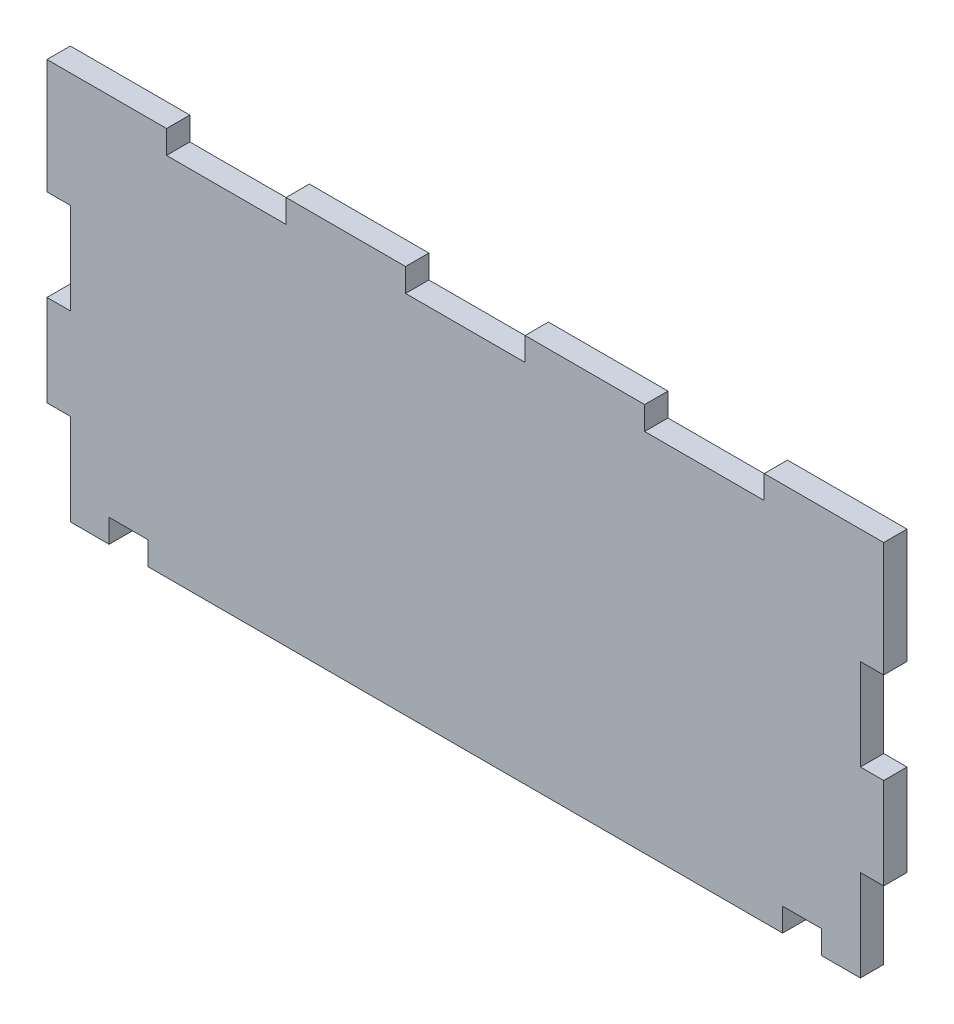
SolidWorks part; units mm, degrees
ref_plane "Alzado" through (0, 0, 0) normal (0, 0, 1) x (1, 0, 0)
ref_plane "Planta" through (0, 0, 0) normal (0, 1, 0) x (1, 0, 0)
ref_plane "Vista lateral" through (0, 0, 0) normal (1, 0, 0) x (0, 0, -1)
sketch "Croquis1" plane through (0, 0, 0) normal (0, 0, 1) x (1, 0, 0)
  line L0 (-76.15, 28.8494) -> (-76.15, -51.02) construction
  line L1 (-79.15, 18.6361) -> (33.46, 18.6361) construction
  line L2 (-79.15, 18.6361) -> (-79.15, -31.3639) construction
  line L3 (-79.15, -31.3639) -> (33.46, -31.3639) construction
  line L4 (33.46, 18.6361) -> (33.46, -31.3639) construction
  line L5 (30.46, 26.8438) -> (30.46, -48.3082) construction
  line L6 (-85.6573, -28.3639) -> (41.9564, -28.3639) construction
  line L7 (-99.0946, 15.6361) -> (68.6346, 15.6361) construction
  line L8 (-71.15, -28.3639) -> (-71.15, -31.3639)
  line L9 (25.46, -28.3639) -> (25.46, -31.3639)
  line L10 (-71.15, -31.3639) -> (25.46, -31.3639)
  line L11 (-71.15, -28.3639) -> (-76.15, -28.3639)
  line L12 (-76.15, -28.3639) -> (-76.15, -31.3639)
  line L13 (-76.15, -31.3639) -> (-79.15, -31.3639)
  line L14 (25.46, -28.3639) -> (30.46, -28.3639)
  line L15 (30.46, -28.3639) -> (30.46, -31.3639)
  line L16 (30.46, -31.3639) -> (33.46, -31.3639)
  line L17 (33.46, -31.3639) -> (33.46, -19.6139)
  line L18 (33.46, -19.6139) -> (30.46, -19.6139)
  line L19 (30.46, -19.6139) -> (30.46, -7.8639)
  line L20 (30.46, -7.8639) -> (33.46, -7.8639)
  line L21 (33.46, -7.8639) -> (33.46, 3.8861)
  line L22 (33.46, 3.8861) -> (30.46, 3.8861)
  line L23 (30.46, 3.8861) -> (30.46, 15.6361)
  line L24 (30.46, 15.6361) -> (15.23, 15.6361)
  line L25 (15.23, 15.6361) -> (15.23, 18.6361)
  line L26 (15.23, 18.6361) -> (0, 18.6361)
  line L27 (0, 18.6361) -> (0, 15.6361)
  line L28 (0, 15.6361) -> (-15.23, 15.6361)
  line L29 (-15.23, 15.6361) -> (-15.23, 18.6361)
  line L30 (-15.23, 18.6361) -> (-30.46, 18.6361)
  line L31 (-30.46, 18.6361) -> (-30.46, 15.6361)
  line L32 (-30.46, 15.6361) -> (-45.69, 15.6361)
  line L33 (-45.69, 15.6361) -> (-45.69, 18.6361)
  line L34 (-45.69, 18.6361) -> (-60.92, 18.6361)
  line L35 (-60.92, 18.6361) -> (-60.92, 15.6361)
  line L36 (-60.92, 15.6361) -> (-76.15, 15.6361)
  line L37 (-79.15, -31.3639) -> (-79.15, -19.6139)
  line L38 (-79.15, -19.6139) -> (-76.15, -19.6139)
  line L39 (-76.15, -19.6139) -> (-76.15, -7.8639)
  line L40 (-76.15, -7.8639) -> (-79.15, -7.8639)
  line L41 (-79.15, -7.8639) -> (-79.15, 3.8861)
  line L42 (-79.15, 3.8861) -> (-76.15, 3.8861)
  line L43 (-76.15, 3.8861) -> (-76.15, 15.6361)
  line L44 (138.6179, 261.633) -> (138.6179, -48.3185) construction
  line L45 (141.6179, 32.5908) -> (141.6179, -48.3185) construction
  line L46 (243.2279, 33.3064) -> (243.2279, -51.0303) construction
  line L47 (246.2279, 143.2673) -> (246.2279, -57.2157) construction
  line L48 (141.6179, -31.3639) -> (146.6179, -31.3639)
  line L49 (141.6179, -31.3639) -> (141.6179, -19.6139)
  line L50 (141.6179, -19.6139) -> (138.6179, -19.6139)
  line L51 (138.6179, -19.6139) -> (138.6179, -7.8639)
  line L52 (138.6179, -7.8639) -> (141.6179, -7.8639)
  line L53 (141.6179, -7.8639) -> (141.6179, 3.8861)
  line L54 (141.6179, 3.8861) -> (138.6179, 3.8861)
  line L55 (138.6179, 3.8861) -> (138.6179, 18.6361)
  line L56 (109.4401, 103.7223) -> (113.3913, 103.7223) construction
  line L57 (138.6179, 211.3323) -> (-4.8813, 211.3323) construction
  line L58 (243.2279, -31.3639) -> (243.2279, -19.6139)
  line L59 (-76.15, 208.3323) -> (30.46, 208.3323) construction
  line L60 (-76.15, 208.3321) -> (-76.15, 106.7221) construction
  line L61 (-76.15, 106.7223) -> (30.46, 106.7223) construction
  line L62 (30.46, 208.3321) -> (30.46, 106.7221) construction
  line L63 (243.2279, -19.6139) -> (246.2279, -19.6139)
  line L64 (246.2279, -19.6139) -> (246.2279, -7.8639)
  line L65 (246.2279, -7.8639) -> (243.2279, -7.8639)
  line L66 (243.2279, -7.8639) -> (243.2279, 3.8861)
  line L67 (243.2279, 3.8861) -> (246.2279, 3.8861)
  line L68 (246.2279, 3.8861) -> (246.2279, 18.6361)
  line L69 (138.6179, 18.6361) -> (153.9908, 18.6361)
  line L70 (153.9908, 18.6361) -> (153.9908, 15.6361)
  line L71 (153.9908, 15.6361) -> (169.3636, 15.6361)
  line L72 (169.3636, 15.6361) -> (169.3636, 18.6361)
  line L73 (169.3636, 18.6361) -> (184.7365, 18.6361)
  line L74 (184.7365, 18.6361) -> (184.7365, 15.6361)
  line L75 (184.7365, 15.6361) -> (200.1093, 15.6361)
  line L76 (200.1093, 15.6361) -> (200.1093, 18.6361)
  line L77 (200.1093, 18.6361) -> (215.4822, 18.6361)
  line L78 (215.4822, 18.6361) -> (215.4822, 15.6361)
  line L79 (215.4822, 15.6361) -> (230.855, 15.6361)
  line L80 (230.855, 15.6361) -> (230.855, 18.6361)
  line L81 (230.855, 18.6361) -> (246.2279, 18.6361)
  line L82 (138.6179, 195.9594) -> (-142.1003, 195.9594) construction
  line L83 (138.6179, 180.5865) -> (-142.1003, 180.5865) construction
  line L84 (138.6179, 165.2137) -> (-133.8306, 165.2137) construction
  line L85 (138.6179, 149.8408) -> (-118.3699, 149.8408) construction
  line L86 (138.6179, 134.468) -> (-142.1003, 134.468) construction
  line L87 (138.6179, 119.0951) -> (-118.3699, 119.0951) construction
  line L88 (30.46, 103.7223) -> (30.46, 119.0951)
  line L89 (30.46, 119.0951) -> (33.46, 119.0951)
  line L90 (33.46, 119.0951) -> (33.46, 134.468)
  line L91 (33.46, 134.468) -> (30.46, 134.468)
  line L92 (30.46, 134.468) -> (30.46, 149.8408)
  line L93 (30.46, 149.8408) -> (33.46, 149.8408)
  line L94 (33.46, 149.8408) -> (33.46, 165.2137)
  line L95 (33.46, 165.2137) -> (30.46, 165.2137)
  line L96 (30.46, 165.2137) -> (30.46, 180.5865)
  line L97 (30.46, 180.5865) -> (33.46, 180.5865)
  line L98 (33.46, 180.5865) -> (33.46, 195.9594)
  line L99 (33.46, 195.9594) -> (30.46, 195.9594)
  line L100 (30.46, 195.9594) -> (30.46, 211.3323)
  line L101 (230.855, 18.6361) -> (230.855, 103.7223) construction
  line L102 (215.4822, 18.6361) -> (215.4822, 103.7223) construction
  line L103 (200.1093, 18.6361) -> (200.1093, 103.7223) construction
  line L104 (184.7365, 18.6361) -> (184.7365, 103.7223) construction
  line L105 (169.3636, 18.6361) -> (169.3636, 103.7223) construction
  line L106 (153.9908, 18.6361) -> (153.9908, 103.7223) construction
  line L107 (15.23, 106.7223) -> (30.46, 106.7223)
  line L108 (15.23, 103.7223) -> (15.23, 106.7223)
  line L109 (15.23, 103.7223) -> (0, 103.7223)
  line L110 (0, 103.7223) -> (0, 106.7223)
  line L111 (0, 106.7223) -> (-15.23, 106.7223)
  line L112 (-15.23, 106.7223) -> (-15.23, 103.7223)
  line L113 (-15.23, 103.7223) -> (-30.46, 103.7223)
  line L114 (-30.46, 103.7223) -> (-30.46, 106.7223)
  line L115 (-30.46, 106.7223) -> (-45.69, 106.7223)
  line L116 (-45.69, 106.7223) -> (-45.69, 103.7223)
  line L117 (-45.69, 103.7223) -> (-60.92, 103.7223)
  line L118 (-60.92, 103.7223) -> (-60.92, 106.7223)
  line L119 (-60.92, 106.7223) -> (-76.15, 106.7223)
  line L120 (-76.15, 106.7223) -> (-76.15, 119.0951)
  line L121 (-76.15, 119.0951) -> (-79.15, 119.0951)
  line L122 (-79.15, 119.0951) -> (-79.15, 134.468)
  line L123 (-79.15, 134.468) -> (-76.15, 134.468)
  line L124 (-76.15, 134.468) -> (-76.15, 149.8408)
  line L125 (-76.15, 149.8408) -> (-79.15, 149.8408)
  line L126 (-79.15, 149.8408) -> (-79.15, 165.2137)
  line L127 (-79.15, 165.2137) -> (-76.15, 165.2137)
  line L128 (-76.15, 165.2137) -> (-76.15, 180.5865)
  line L129 (-76.15, 180.5865) -> (-79.15, 180.5865)
  line L130 (-79.15, 180.5865) -> (-79.15, 195.9594)
  line L131 (-79.15, 195.9594) -> (-76.15, 195.9594)
  line L132 (-76.15, 195.9594) -> (-76.15, 208.3323)
  line L133 (-76.15, 208.3323) -> (-60.92, 208.3323)
  line L134 (-60.92, 208.3323) -> (-60.92, 211.3323)
  line L135 (-60.92, 211.3323) -> (-45.69, 211.3323)
  line L136 (-45.69, 211.3323) -> (-45.69, 208.3323)
  line L137 (-45.69, 208.3323) -> (-30.46, 208.3323)
  line L138 (-30.46, 208.3323) -> (-30.46, 211.3323)
  line L139 (-30.46, 211.3323) -> (-15.23, 211.3323)
  line L140 (-15.23, 211.3323) -> (-15.23, 208.3323)
  line L141 (-15.23, 208.3323) -> (0, 208.3323)
  line L142 (0, 208.3323) -> (0, 211.3323)
  line L143 (0, 211.3323) -> (15.23, 211.3323)
  line L144 (15.23, 211.3323) -> (15.23, 208.3323)
  line L145 (15.23, 208.3323) -> (30.46, 208.3323)
  line L146 (30.46, 106.7223) -> (30.46, 119.0951)
  line L147 (151.6179, -31.3639) -> (151.6179, -28.3639)
  line L148 (151.6179, -28.3639) -> (146.6179, -28.3639)
  line L149 (146.6179, -28.3639) -> (146.6179, -31.3639)
  line L150 (233.2279, -31.3639) -> (233.2279, -28.3639)
  line L151 (233.2279, -28.3639) -> (238.2279, -28.3639)
  line L152 (238.2279, -28.3639) -> (238.2279, -31.3639)
  line L153 (151.6179, -31.3639) -> (233.2279, -31.3639)
  line L154 (238.2279, -31.3639) -> (243.2279, -31.3639)
  arc A0 (246.2279, 103.7223) -> (138.6179, 211.3323) centre (138.6179, 103.7223) ccw construction
  arc A1 (230.855, 103.7223) -> (138.6179, 195.9594) centre (138.6179, 103.7223) ccw construction
  arc A2 (215.4822, 103.7223) -> (138.6179, 180.5865) centre (138.6179, 103.7223) ccw construction
  arc A3 (200.1093, 103.7223) -> (138.6179, 165.2137) centre (138.6179, 103.7223) ccw construction
  arc A4 (184.7365, 103.7223) -> (138.6179, 149.8408) centre (138.6179, 103.7223) ccw construction
  arc A5 (169.3636, 103.7223) -> (138.6179, 134.468) centre (138.6179, 103.7223) ccw construction
  arc A6 (153.9908, 103.7223) -> (138.6179, 119.0951) centre (138.6179, 103.7223) ccw construction
  dimension "D1" = 112.61
  dimension "D2" = 3
  dimension "D3" = 3
  dimension "D4" = 3
  dimension "D5" = 3
  dimension "D6" = 3
  dimension "D7" = 5
  dimension "D8" = 5
  dimension "D9" = 3
  dimension "D10" = 3
  dimension "D11" = 107.61
  dimension "D12" = 3
  dimension "D13" = 3
  dimension "D14" = 3
  dimension "D15" = 3
  dimension "D16" = 5
  dimension "D17" = 5
  dimension "D18" = 5
  dimension "D19" = 5
extrude "Saliente-Extruir1" add sketch "Croquis1" along normal blind 3
